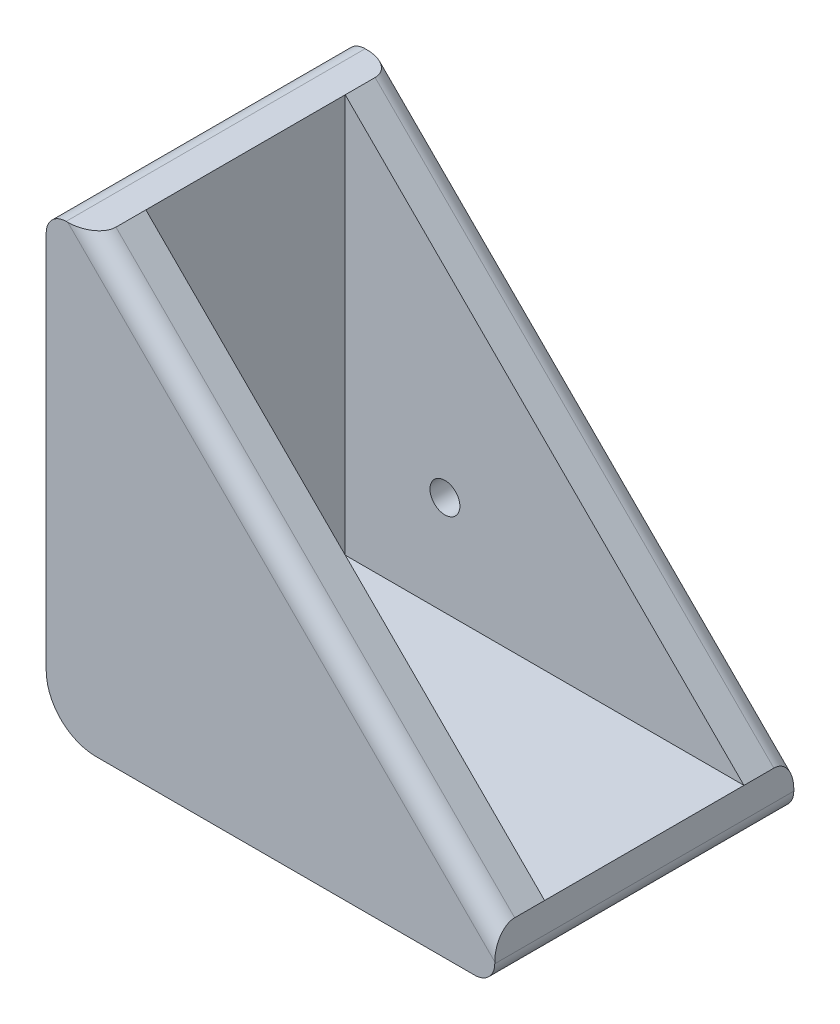
SolidWorks part; units mm, degrees
ref_plane "Front Plane" through (0, 0, 0) normal (0, 0, 1) x (1, 0, 0)
ref_plane "Top Plane" through (0, 0, 0) normal (0, 1, 0) x (1, 0, 0)
ref_plane "Right Plane" through (0, 0, 0) normal (1, 0, 0) x (0, 0, -1)
sketch "Sketch1" plane through (0, 0, 0) normal (0, 0, 1) x (1, 0, 0)
  line L0 (0, 0) -> (0, 45)
  line L1 (0, 45) -> (5, 45)
  line L2 (5, 45) -> (5, 5)
  line L3 (5, 5) -> (45, 5)
  line L4 (45, 5) -> (45, 0)
  line L5 (45, 0) -> (0, 0)
  dimension "D1" = 45
  dimension "D2" = 45
  dimension "D3" = 5
  dimension "D4" = 5
extrude "Boss-Extrude2" add sketch "Sketch1" along normal blind 30
sketch "Sketch2" plane through (0, 0, 30) normal (0, 0, 1) x (1, 0, 0)
  line L0 (5, 45) -> (45, 5)
  line L1 (45, 5) -> (5, 5)
  line L2 (5, 5) -> (5, 45)
extrude "Boss-Extrude3" add sketch "Sketch2" against normal blind 5
sketch "Sketch3" plane through (0, 0, 0) normal (0, 0, -1) x (-1, 0, 0)
  line L0 (-5, 45) -> (-5, 5)
  line L1 (-5, 5) -> (-45, 5)
  line L2 (-45, 5) -> (-5, 45)
extrude "Boss-Extrude4" add sketch "Sketch3" against normal blind 5
sketch "Sketch4" plane through (0, 0, 0) normal (0, -1, 0) x (1, 0, 0)
  line L0 (5, 25) -> (45, 25) construction
  line L1 (5, 25) -> (5, 5) construction
  circle A0 centre (15, 15) radius 1.5
  dimension "D1" = 3
  dimension "D2" = 10
  dimension "D3" = 10
extrude "Cut-Extrude1" cut sketch "Sketch4" against normal through all
sketch "Sketch5" plane through (0, 0, 5) normal (0, 0, 1) x (1, 0, 0)
  line L0 (5, 5) -> (5, 45) construction
  line L1 (45, 5) -> (5, 5) construction
  circle A0 centre (15, 15) radius 1.5
  dimension "D1" = 3
  dimension "D2" = 10
  dimension "D3" = 10
extrude "Cut-Extrude2" cut sketch "Sketch5" against normal through all
fillet "Fillet1" radius 2 4 edges at (25, 25, 0) (25, 25, 30) (0, 45, 15) (45, 0, 15)
fillet "Fillet2" radius 5 1 edges at (0, 0, 15)
